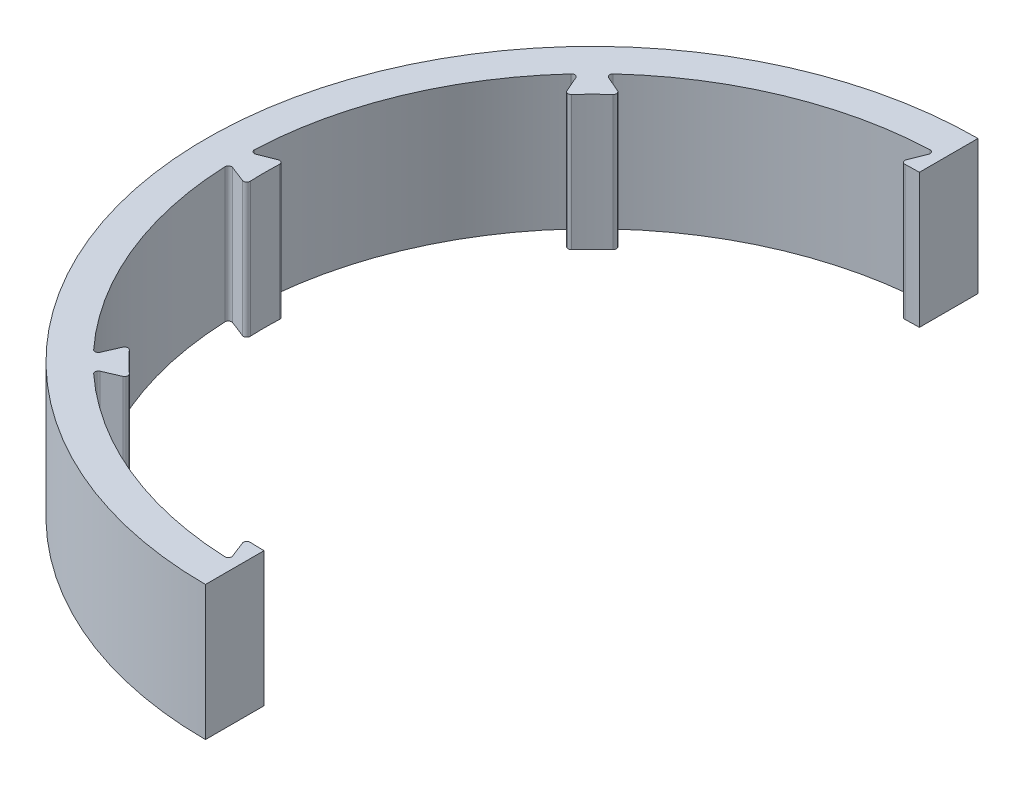
SolidWorks part; units mm, degrees
ref_plane "Front Plane" through (0, 0, 0) normal (0, 0, 1) x (1, 0, 0)
ref_plane "Top Plane" through (0, 0, 0) normal (0, 1, 0) x (1, 0, 0)
ref_plane "Right Plane" through (0, 0, 0) normal (1, 0, 0) x (0, 0, -1)
sketch "Sketch1" plane through (0, 0, 0) normal (0, 1, 0) x (1, 0, 0)
  circle A0 centre (0, 0) radius 115
  circle A1 centre (0, 0) radius 105.05
  dimension "D1" = 230
  dimension "D2" = 210.1
extrude "Boss-Extrude1" add sketch "Sketch1" along normal blind 40
sketch "Sketch2" plane through (0, 40, 0) normal (0, 1, 0) x (1, 0, 0)
  line L0 (-3, 105.0072) -> (-6, 97.3653)
  line L1 (3, 105.0072) -> (6, 97.3653)
  line L2 (2.8914, 105.0102) -> (5.8899, 97.372)
  line L3 (-2.8914, 105.0102) -> (-5.8899, 97.372)
  circle A0 centre (0, 0) radius 105.05
  circle A3 centre (0, 0) radius 105.05 construction
  circle A4 centre (0, 0) radius 97.55
  circle M8 centre (0, 0) radius 105.05
  dimension "D1" = 195.1
  dimension "D3" = 3
  dimension "D4" = 3
  dimension "D5" = 3
  dimension "D2" = 3
  dimension "D6" = 0.1
  dimension "D7" = 0.1
extrude "Boss-Extrude2" add sketch "Sketch2" against normal through all contours A4 L1 L0 M8
fillet "Fillet2" radius 1 4 edges at (-2.8914, 20, -105.0102) (-5.8899, 20, -97.372) (5.8899, 20, -97.372) (2.8914, 20, -105.0102)
pattern_circular "CirPattern2" count 8 over 360 about axis through (0, 0, 0) along (0, 1, 0) of "Fillet2", "Boss-Extrude2"
sketch "Sketch3" plane through (0, 40, 0) normal (0, 1, 0) x (1, 0, 0)
  line L1 (-0.05, -119.9497) -> (-0.15, -119.9497)
  line L2 (-0.15, -117.3494) -> (-0.15, 117.3494)
  circle A0 centre (-0.15, 0) radius 117.3494
  point P8 (0, 0)
  dimension "D1" = 0.15
extrude "Cut-Extrude2" cut sketch "Sketch3" against normal through all contours L2 A0
